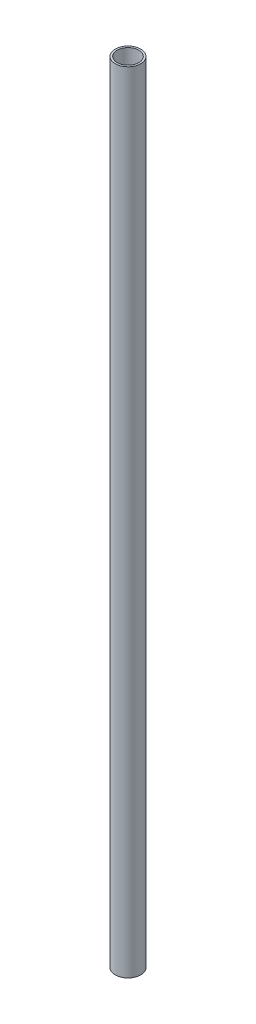
SolidWorks part; units mm, degrees
ref_plane "Front" through (0, 0, 0) normal (0, 0, 1) x (1, 0, 0)
ref_plane "Top" through (0, 0, 0) normal (0, 1, 0) x (1, 0, 0)
ref_plane "Right" through (0, 0, 0) normal (1, 0, 0) x (0, 0, -1)
sketch "Sketch1" plane through (0, 0, 0) normal (0, 1, 0) x (1, 0, 0)
  circle A0 centre (0, 0) radius 20
  dimension "D1" = 40
extrude "Boss-Extrude1" add sketch "Sketch1" along normal blind 1240
sketch "Sketch2" plane through (0, 1240, 0) normal (0, 1, 0) x (1, 0, 0)
  circle A0 centre (0, 0) radius 17
  dimension "D1" = 34
extrude "Cut-Extrude1" cut sketch "Sketch2" against normal up to next
